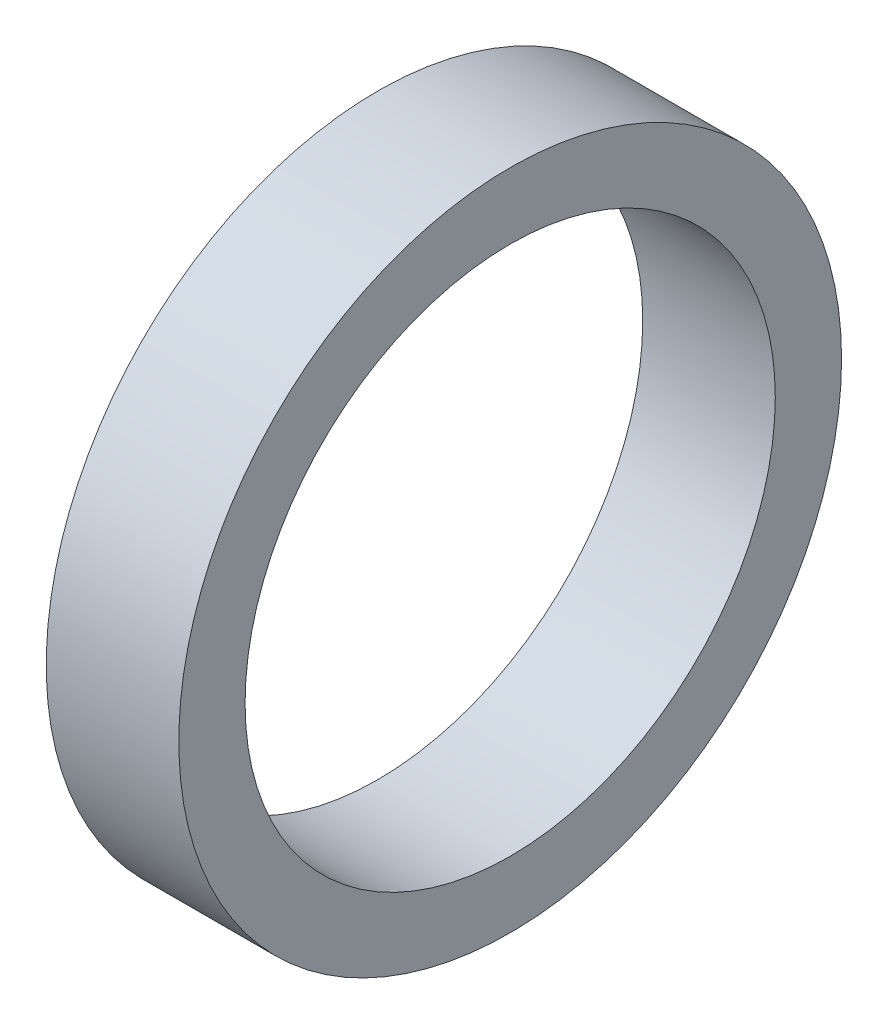
SolidWorks part; units mm, degrees
ref_plane "Спереди" through (0, 0, 0) normal (0, 0, 1) x (1, 0, 0)
ref_plane "Сверху" through (0, 0, 0) normal (0, 1, 0) x (1, 0, 0)
ref_plane "Справа" through (0, 0, 0) normal (1, 0, 0) x (0, 0, -1)
sketch "Эскиз3" plane through (0, 0, 0) normal (1, 0, 0) x (0, 0, -1)
  circle A0 centre (0, 0) radius 2.5
  dimension "D1" = 5
extrude "Бобышка-Вытянуть2" add sketch "Эскиз3" along normal blind 1
sketch "Эскиз4" plane through (1, 0, 0) normal (1, 0, 0) x (0, 0, -1)
  circle A0 centre (0, 0) radius 2
  dimension "D1" = 4
extrude "Вырез-Вытянуть1" cut sketch "Эскиз4" against normal blind 1
